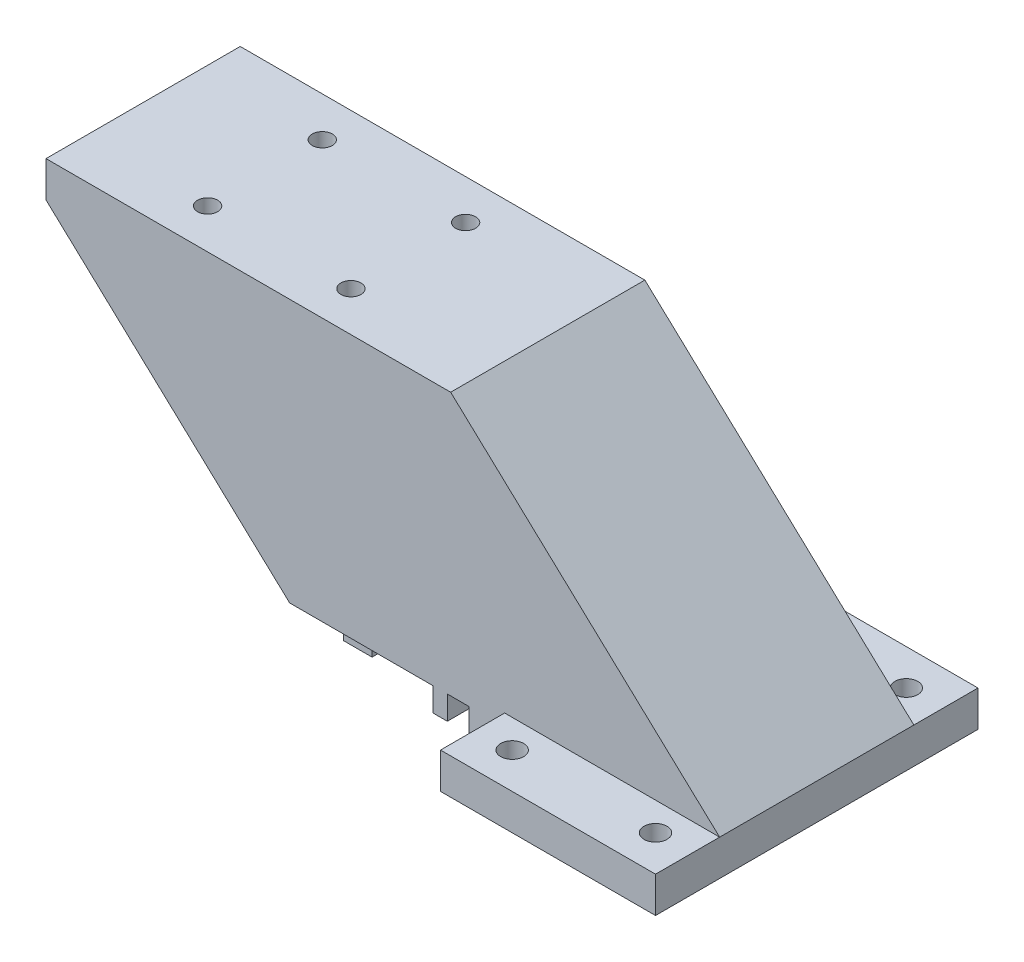
SolidWorks part; units mm, degrees
ref_plane "Front Plane" through (0, 0, 0) normal (0, 0, 1) x (1, 0, 0)
ref_plane "Top Plane" through (0, 0, 0) normal (0, 1, 0) x (1, 0, 0)
ref_plane "Right Plane" through (0, 0, 0) normal (1, 0, 0) x (0, 0, -1)
sketch "Sketch1" plane through (0, 0, 0) normal (0, 1, 0) x (1, 0, 0)
  line L1 (-15, 22.5) -> (15, 22.5)
  line L2 (-15, 22.5) -> (-15, -22.5)
  line L3 (-15, -22.5) -> (15, -22.5)
  line L4 (15, 22.5) -> (15, -22.5)
  line L5 (-15, 22.5) -> (15, -22.5) construction
  line L6 (-15, -22.5) -> (15, 22.5) construction
  line L7 (-6, 22.5) -> (6, 22.5)
  circle A0 centre (-10, 17.5) radius 1.6
  circle A1 centre (10, 17.5) radius 1.6
  circle A2 centre (10, -17.5) radius 1.6
  circle A3 centre (-10, -17.5) radius 1.6
  point P0 (0, 0)
  dimension "D3" = 5
  dimension "D4" = 5
  dimension "D5" = 3.2
  dimension "D8" = 5
  dimension "D9" = 5
  dimension "D10" = 5
  dimension "D1" = 30
  dimension "D2" = 45
  dimension "D6" = 2
  dimension "D7" = 2
extrude "Boss-Extrude3" add sketch "Sketch1" along normal blind 5
sketch "Sketch2" plane through (0, 5, 0) normal (0, 1, 0) x (1, 0, 0)
  line L0 (15, 22.5) -> (15, -22.5) construction
  line L1 (15, -13.55) -> (-15, -13.55)
  line L2 (15, -13.55) -> (15, 13.55)
  line L3 (15, 13.55) -> (-15, 13.55)
  line L4 (-15, -13.55) -> (-15, 13.55)
  line L5 (-15, 22.5) -> (-15, -22.5) construction
  line L7 (-15, 13.55) -> (-79, 13.55)
  line L8 (-15, 13.55) -> (-15, -13.55)
  line L9 (-15, -13.55) -> (-79, -13.55)
  line L10 (-79, 13.55) -> (-79, -13.55)
  circle A3 centre (10, 17.5) radius 1.6 construction
  circle A7 centre (10, -17.5) radius 1.6 construction
  line M8 (15, -22.5) -> (15, 22.5)
  line M14 (-15, 22.5) -> (-15, -22.5)
  dimension "D2" = 3.95
  dimension "D1" = 3.95
  dimension "D3" = 64
extrude "Boss-Extrude4" add sketch "Sketch2" along normal blind 35 and the other way blind 1.7 contours L7 L10 L9 M14 | L3 L1 M8 M14
sketch "Sketch3" plane through (0, 3.3, 0) normal (0, -1, 0) x (1, 0, 0)
  line L4 (-40, 11.05) -> (-40, -13.55)
  line L5 (-15, -13.55) -> (-79, -13.55) construction
  line L6 (-15, -22.5) -> (-15, 22.5) construction
  line L7 (-15, 13.55) -> (-79, 13.55) construction
  line L8 (-40, 11.05) -> (-36, 11.05)
  line L9 (-40, 11.05) -> (-40, -13.55)
  line L10 (-40, -13.55) -> (-36, -13.55)
  line L11 (-36, 11.05) -> (-36, -13.55)
  line L12 (-20, 13.55) -> (-15, 13.55)
  line L13 (-20, 13.55) -> (-20, -13.55)
  line L14 (-20, -13.55) -> (-15, -13.55)
  line L15 (-15, 13.55) -> (-15, -13.55)
  line L17 (-25, 13.55) -> (-23, 13.55)
  line L18 (-25, 13.55) -> (-25, -13.55)
  line L19 (-25, -13.55) -> (-23, -13.55)
  line L20 (-23, 13.55) -> (-23, -13.55)
  line M2 (-79, -13.55) -> (-15, -13.55)
  line M3 (-15, -13.55) -> (-15, 13.55)
  line M4 (-15, 13.55) -> (-79, 13.55)
  dimension "D1" = 25
  dimension "D2" = 4
  dimension "D3" = 5
  dimension "D4" = 2
  dimension "D5" = 3
extrude "Boss-Extrude5" add sketch "Sketch3" along normal blind 3.3 contours L11 L4 M4 M2 | L13 M4 M2 M3 | L20 L18 M4 M2
sketch "Sketch4" plane through (0, 40, 0) normal (0, 1, 0) x (1, 0, 0)
  line L0 (15, 13.55) -> (-79, 13.55) construction
  line L1 (-79, 13.55) -> (-79, -13.55) construction
  line L2 (-62, 8) -> (-42, 8) construction
  line L3 (-42, 8) -> (-52, 8) construction
  line L4 (-52, 8) -> (-52, 13.55) construction
  line L5 (-52, 13.55) -> (-52, -13.55) construction
  line L6 (15, -13.55) -> (-79, -13.55) construction
  line L7 (-52, 0) -> (-46.2014, 0) construction
  circle A0 centre (-62, 8) radius 1.4
  circle A1 centre (-42, 8) radius 1.4
  circle A2 centre (-42, -8) radius 1.4
  circle A3 centre (-62, -8) radius 1.4
  dimension "D1" = 2.8
  dimension "D2" = 8
  dimension "D3" = 17
  dimension "D6" = 20
  dimension "D7" = 16
  dimension "D8" = 16
  dimension "D4" = 2
  dimension "D5" = 2
extrude "Cut-Extrude1" cut sketch "Sketch4" against normal through all
ref_plane "Plane1" through (0, 0, 0) normal (0, 0, -1) x (-1, 0, 0)
sketch "Sketch7" plane through (0, 0, 13.55) normal (0, 0, 1) x (1, 0, 0)
  line L0 (-79, 40) -> (-79, 35)
  line L1 (-79, 3.3) -> (-79, 40) construction
  line L2 (-40, 3.3) -> (-45, 3.3)
  line L4 (-25, 3.3) -> (-79, 3.3) construction
  line L5 (-79, 35) -> (-45, 3.3)
  line L6 (-79, 3.3) -> (-45, 3.3)
  line L7 (-79, 3.3) -> (-79, 35)
  line M11 (-79, 40) -> (-79, 3.3)
  line M12 (-79, 3.3) -> (-25, 3.3)
  dimension "D1" = 5
  dimension "D2" = 5
extrude "Cut-Extrude4" cut sketch "Sketch7" against normal through all contours L5 M11 M12
sketch "Sketch8" plane through (0, 0, 0) normal (0, 0, -1) x (-1, 0, 0)
  line L0 (40, 3.3) -> (45, 3.3) construction
  line L1 (79, 35) -> (34, 35)
  line L2 (79, 35) -> (79, 8.3)
  line L3 (79, 8.3) -> (51.3065, 8.3)
  line L4 (34, 35) -> (34, 8.3)
  line L6 (40, 8.3) -> (34, 8.3)
  line L11 (40, 3.3) -> (51.3065, 3.3)
  line L12 (40, 3.3) -> (40, 8.3)
  line L14 (51.3065, 3.3) -> (51.3065, 8.3)
  dimension "D1" = 5
  dimension "D2" = 45
extrude "Cut-Extrude5" cut sketch "Sketch8" against normal blind 10 and the other way blind 10
sketch "Sketch9" plane through (0, 0, -13.55) normal (0, 0, -1) x (-1, 0, 0)
  line L0 (-15, 5) -> (22.5329, 40)
  line L1 (-15, 40) -> (79, 40) construction
  line L4 (15, 5) -> (-15, 5) construction
  line L6 (-15, 40) -> (22.5329, 40)
  line L7 (-15, 40) -> (-15, 5)
  line L8 (-15, 5) -> (22.5329, 5)
  line L9 (22.5329, 40) -> (22.5329, 5)
  line M5 (79, 40) -> (-15, 40)
  line M6 (-15, 40) -> (-15, 5)
  dimension "D1" = 137
extrude "Cut-Extrude6" cut sketch "Sketch9" against normal through all contours L0 M6 M5
